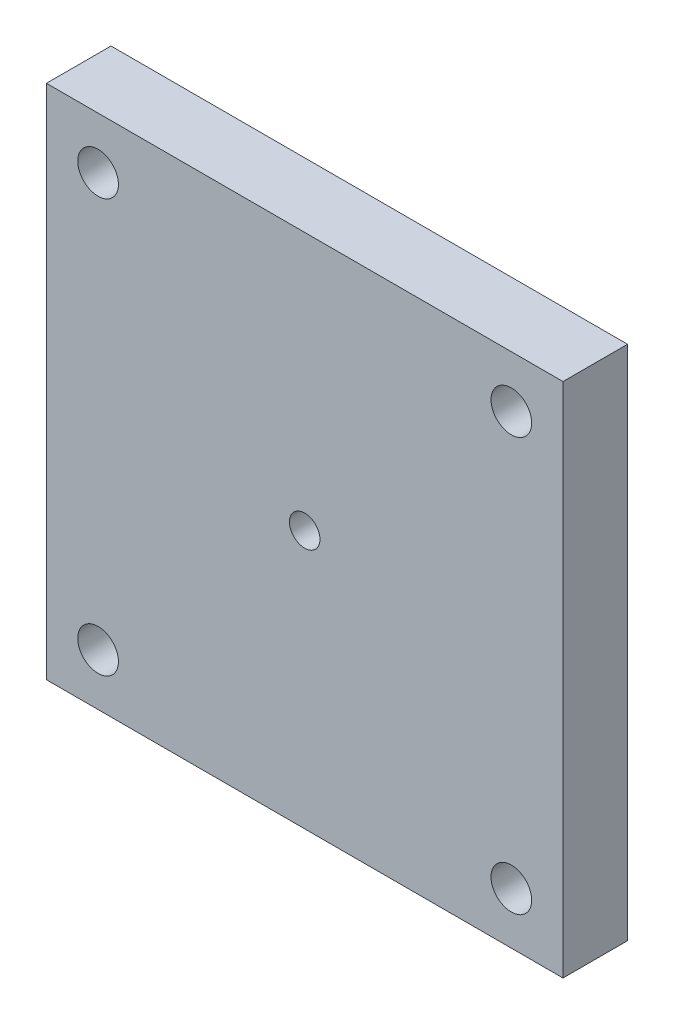
SolidWorks part; units mm, degrees
ref_plane "Front Plane" through (0, 0, 0) normal (0, 0, 1) x (1, 0, 0)
ref_plane "Top Plane" through (0, 0, 0) normal (0, 1, 0) x (1, 0, 0)
ref_plane "Right Plane" through (0, 0, 0) normal (1, 0, 0) x (0, 0, -1)
sketch "Sketch2" plane through (0, 0, 0) normal (0, 0, 1) x (1, 0, 0)
  line L1 (0, 0) -> (50.8, 0)
  line L2 (0, 0) -> (0, 50.8)
  line L3 (0, 50.8) -> (50.8, 50.8)
  line L4 (50.8, 0) -> (50.8, 50.8)
  circle A0 centre (5.08, 45.72) radius 2
  circle A1 centre (45.72, 45.72) radius 2
  circle A2 centre (45.72, 5.08) radius 2
  circle A3 centre (5.08, 5.08) radius 2
  circle A4 centre (25.4, 25.4) radius 1.4986
  dimension "D3" = 4
  dimension "D6" = 2.9972
  dimension "D7" = 5.08
  dimension "D8" = 5.08
  dimension "D1" = 50.8
  dimension "D2" = 50.8
  dimension "D4" = 5.08
  dimension "D5" = 5.08
extrude "Boss-Extrude1" add sketch "Sketch2" along normal blind 6.35
